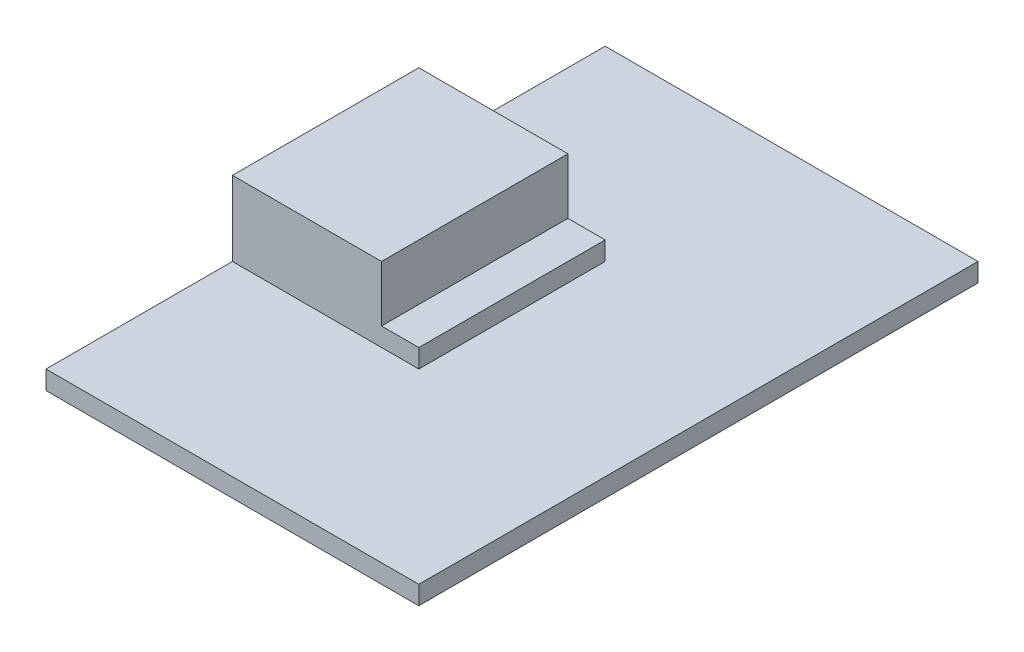
SolidWorks part; units mm, degrees
ref_plane "Piano frontale" through (0, 0, 0) normal (0, 0, 1) x (1, 0, 0)
ref_plane "Piano superiore" through (0, 0, 0) normal (0, 1, 0) x (1, 0, 0)
ref_plane "Piano destro" through (0, 0, 0) normal (1, 0, 0) x (0, 0, -1)
sketch "Schizzo1" plane through (0, 0, 0) normal (0, 1, 0) x (1, 0, 0)
  line L1 (4, 5) -> (-4, 5)
  line L2 (4, 5) -> (4, -5)
  line L3 (4, -5) -> (-4, -5)
  line L4 (-4, 5) -> (-4, -5)
  line L5 (4, 5) -> (-4, -5) construction
  line L6 (4, -5) -> (-4, 5) construction
  point P0 (0, 0)
  dimension "D1" = 8
  dimension "D2" = 10
extrude "Estrusione-Estrusione1" add sketch "Schizzo1" along normal blind 5
sketch "Schizzo2" plane through (4, 0, 0) normal (1, 0, 0) x (0, 0, -1)
  line L0 (5, 5) -> (5, 0) construction
  line L1 (-5, 0) -> (5, 0)
  line L2 (-5, 0) -> (-5, 2)
  line L3 (-5, 2) -> (5, 2)
  line L4 (5, 0) -> (5, 2)
  dimension "D1" = 2
extrude "Estrusione-Estrusione2" add sketch "Schizzo2" along normal blind 2
sketch "Schizzo3" plane through (0, 0, 0) normal (0, -1, 0) x (1, 0, 0)
  line L1 (-4, 15) -> (16, 15)
  line L2 (-4, 15) -> (-4, -15)
  line L3 (-4, -15) -> (16, -15)
  line L4 (16, 15) -> (16, -15)
  dimension "D1" = 30
  dimension "D2" = 15
  dimension "D3" = 20
extrude "Estrusione-Estrusione3" add sketch "Schizzo3" against normal blind 1
sketch "Schizzo5" plane through (0, 0, 0) normal (0, -1, 0) x (1, 0, 0)
  line L0 (-4, 0) -> (16, 0) construction
  line L1 (-4, -15) -> (-4, 15) construction
  line L2 (16, -15) -> (16, 15) construction
